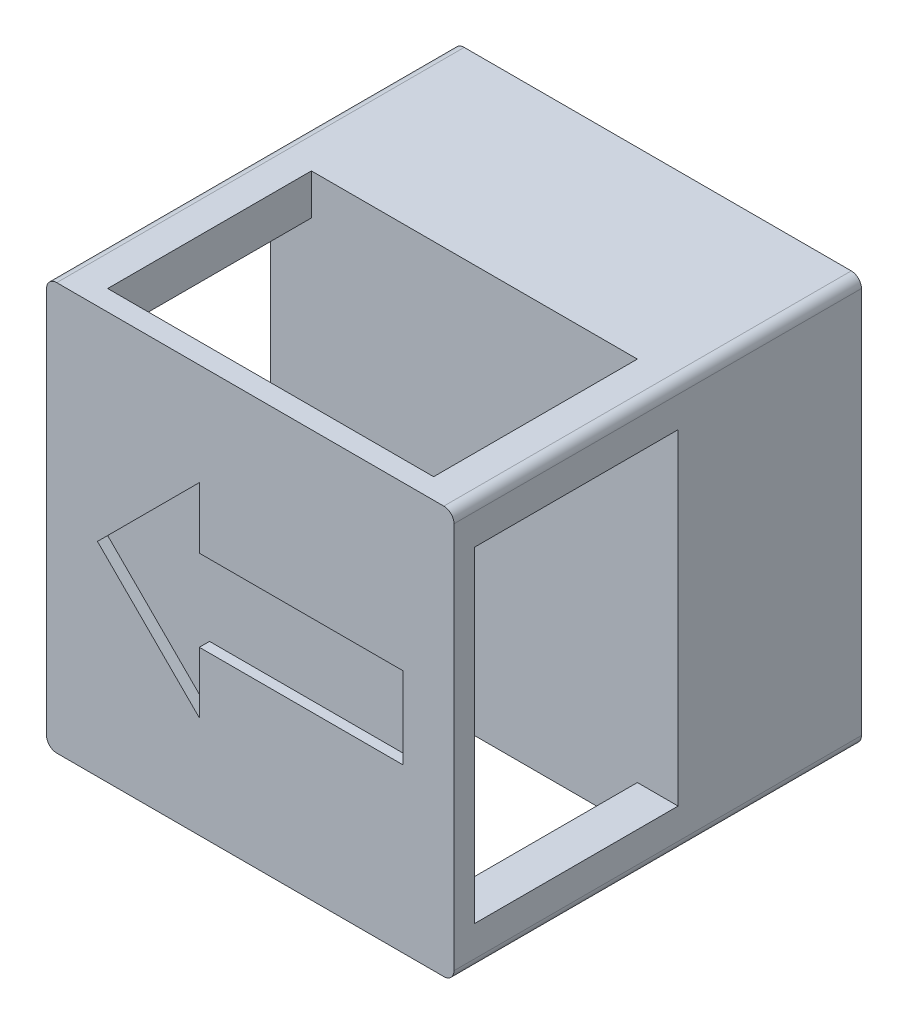
SolidWorks part; units mm, degrees
ref_plane "Front Plane" through (0, 0, 0) normal (0, 0, 1) x (1, 0, 0)
ref_plane "Top Plane" through (0, 0, 0) normal (0, 1, 0) x (1, 0, 0)
ref_plane "Right Plane" through (0, 0, 0) normal (1, 0, 0) x (0, 0, -1)
sketch "Sketch1" plane through (0, 0, 0) normal (0, 0, 1) x (1, 0, 0)
  line L1 (-200, -200) -> (200, -200)
  line L2 (-200, -200) -> (-200, 200)
  line L3 (-200, 200) -> (200, 200)
  line L4 (200, -200) -> (200, 200)
  line L5 (-200, -200) -> (200, 200) construction
  line L6 (-200, 200) -> (200, -200) construction
  point P0 (0, 0)
  dimension "D1" = 400
  dimension "D2" = 400
extrude "Boss-Extrude1" add sketch "Sketch1" along normal blind 400
ref_plane "Plane1" through (0, 0, 380) normal (0, 0, 1) x (1, 0, 0)
sketch "Sketch2" plane through (0, 0, 380) normal (0, 0, 1) x (1, 0, 0)
  line L1 (-200, 200) -> (-160, 200)
  line L2 (-200, 200) -> (-200, 160)
  line L3 (-200, 160) -> (-160, 160)
  line L4 (200, -200) -> (200, 200)
  line L5 (200, 200) -> (-200, 200)
  line L6 (-200, 200) -> (-200, -200)
  line L7 (-200, -200) -> (200, -200)
  line L8 (200, -200) -> (200, 200)
  line L9 (200, 200) -> (-200, 200)
  line L10 (-200, 200) -> (-200, -200)
  line L11 (-200, -200) -> (200, -200)
  line L12 (-160, 200) -> (-160, 160)
  line L13 (200, 200) -> (160, 200)
  line L14 (200, 200) -> (200, 160)
  line L15 (200, 160) -> (160, 160)
  line L16 (160, 200) -> (160, 160)
  line L17 (-200, -200) -> (-160, -200)
  line L18 (-200, -200) -> (-200, -160)
  line L19 (-200, -160) -> (-160, -160)
  line L20 (-160, -200) -> (-160, -160)
  line L21 (200, -200) -> (160, -200)
  line L22 (200, -200) -> (200, -160)
  line L23 (200, -160) -> (160, -160)
  line L24 (160, -200) -> (160, -160)
  dimension "D2" = 40
  dimension "D1" = 0
extrude "Cut-Extrude1" cut sketch "Sketch2" against normal blind 200 contours L11 L24 L23 L8 L15 L16 L9 L12 L3 L10 L19 L20
sketch "Sketch3" plane through (0, 0, 400) normal (0, 0, 1) x (1, 0, 0)
  line L1 (-200, 0) -> (410.6331, 0) construction
  line L2 (-200, 200) -> (-200, -200) construction
  line L3 (-150, 0) -> (-50, 100)
  line L4 (-50, 100) -> (-50, 40)
  line L5 (-50, 40) -> (150, 40)
  line L6 (150, 40) -> (150, -40)
  line L7 (150, -40) -> (-50, -40)
  line L8 (-50, -40) -> (-50, -100)
  line L9 (-50, -100) -> (-150, 0)
  line L10 (200, -200) -> (200, 200) construction
  point P11 (150, 0)
  dimension "D1" = 200
  dimension "D2" = 100
  dimension "D3" = 50
  dimension "D4" = 50
  dimension "D5" = 80
extrude "Cut-Extrude2" cut sketch "Sketch3" against normal blind 10
fillet "Fillet1" radius 10 4 edges at (200, 200, 200) (-200, 200, 200) (-200, -200, 200) (200, -200, 200)
